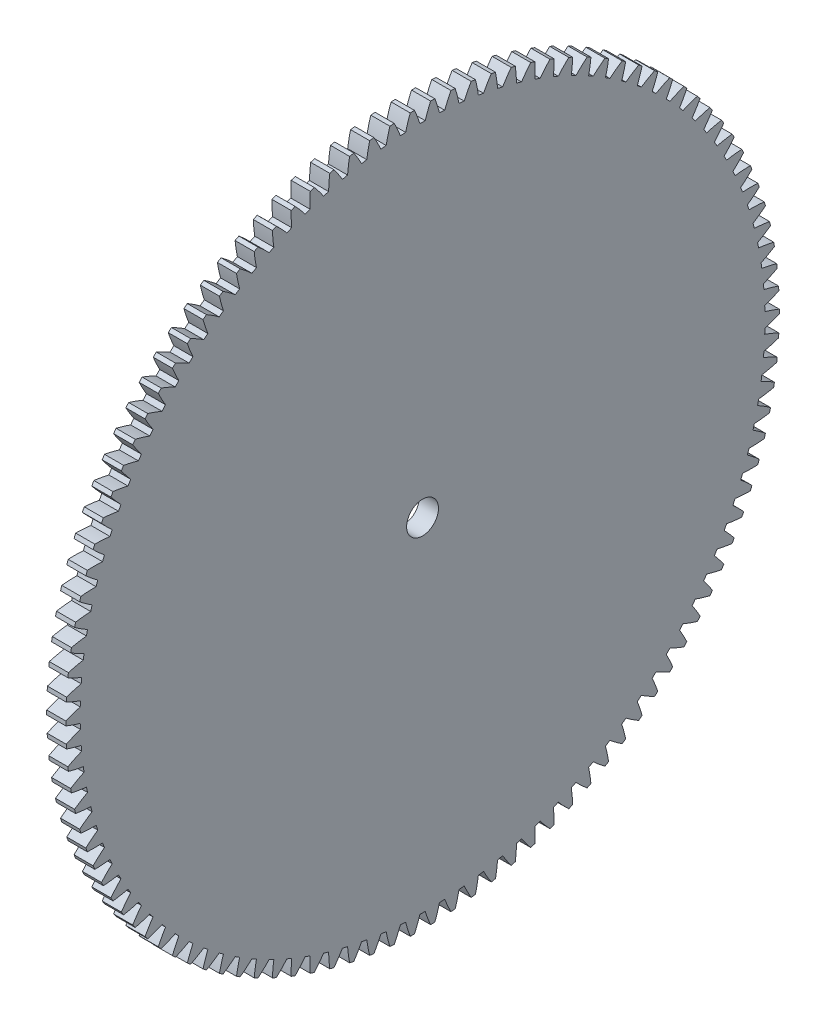
SolidWorks part; units mm, degrees
ref_plane "Plane1" through (0, 0, 0) normal (0, 0, 1) x (1, 0, 0)
ref_plane "Plane2" through (0, 0, 0) normal (0, 1, 0) x (1, 0, 0)
ref_plane "Plane3" through (0, 0, 0) normal (1, 0, 0) x (0, 0, -1)
sketch "HoldingSke" plane through (0, 0, 0) normal (0, 1, 0) x (1, 0, 0)
  line L0 (0, 0) -> (-0.342, -0.9397)
  line L1 (-15, 0) -> (100, 0) construction
  line L2 (0, 0) -> (-2.1039, 2.3779)
  line L3 (0, 0) -> (-11.863, 4.5341)
  line L4 (0, 0) -> (-2.9537, 8.1152)
  line L5 (0, 0) -> (-46.8476, -17.4728)
  line L6 (0, 0) -> (-2.4869, -1.6779)
  line L7 (-2.1039, 2.3779) -> (8.6586, 51.2059)
  line L8 (-76.2, 54.61) -> (-75.3, 54.61)
  line L9 (-71.009, 38.7566) -> (-53.1078, 45.2721)
  line L10 (-76.2, 71.12) -> (104.1128, 71.12)
  line L11 (0, 0) -> (-3, 0)
  line L12 (-76.2, 101.6) -> (-76.162, 101.6)
  line L13 (24.9733, 27.94) -> (52.9518, 28.4284)
  line L14 (24.9733, 27.94) -> (24.9743, 27.94)
  line L15 (24.9733, 27.94) -> (100.4006, 29.5858)
  line L16 (-63.627, -1) -> (-12.827, -1)
  circle A0 centre (0, 0) radius 2.5
  circle A1 centre (0, 0) radius 37.5
  circle A2 centre (0, 0) radius 37.5
  circle A3 centre (0, 0) radius 2.5
  dimension "MHD" = 75
  dimension "Hub_dia" = 75
  dimension "Bore" = 5
  dimension "MBD" = 5
  dimension "Num_teeth" = 110
  dimension "Pitch_radius" = 180.3128
  dimension "Pitch" = 1
  dimension "Width" = 3
  dimension "Overall_len" = 50
  dimension "Show_teeth" = 110
  dimension "Thickness" = 3
  dimension "OAL" = 50.0001
  dimension "T_dim" = 0.9
  dimension "Ap" = 20
  dimension "H" = 19.05
  dimension "Backlash" = 0.038
  dimension "Addendum_fac" = 1
  dimension "Dedendum_fac" = 1.25
  dimension "Clearance_fac" = 0.25
  dimension "Dedendum_add" = 0.001
  dimension "Module" = 1
sketch "BasProSke" plane through (0, 0, 0) normal (0, 1, 0) x (1, 0, 0)
  line L0 (-10, 0) -> (60, 0) construction
  line L1 (0, 0) -> (0, 56)
  line L2 (0, 0) -> (3, 0)
  line L3 (3, 0) -> (3, 56)
  line L4 (3, 56) -> (0, 56)
  dimension "Diameter" = 112
  dimension "Thickness" = 3
revolve "Base-Revolve" add sketch "BasProSke" angle 360 about L0
sketch "TooCutSke" plane through (0, 0, 0) normal (1, 0, 0) x (0, 0, -1)
  line L1 (0, 0) -> (0, 107) construction
  line L2 (0, 0) -> (-0.8519, 54.9934) construction
  line L3 (0, 0) -> (-3.1409, 109.9457) construction
  line L4 (-0.8519, 54.9934) -> (-1.5704, 54.9729) construction
  arc A0 (0.4125, 53.7474) -> (-0.4125, 53.7474) centre (0, 0) ccw
  arc A1 (1.275, 56.0109) -> (-1.275, 56.0109) centre (0, 0) ccw
  circle A2 centre (0, 0) radius 55 construction
  circle A3 centre (0, 0) radius 51.6831 construction
  arc A4 (-0.4125, 53.7474) -> (-1.275, 56.0109) centre (-21.3708, 47.0578) ccw
  arc A5 (1.275, 56.0109) -> (0.4125, 53.7474) centre (21.3708, 47.0578) ccw
  dimension "Root_dia" = 107.498
  dimension "Overcut_dia" = 112.0508
  dimension "Pitch_dia" = 110
  dimension "Base_dia" = 103.3662
  dimension "Flank_rad" = 22
  dimension "Half_ang" = 1.636
  dimension "Half_CT" = 0.7189
extrude "ToothCut" cut sketch "TooCutSke" along normal through all
fillet "Breaks" [suppressed] radius 0.02
fillet "RootFillets" [suppressed] radius 0.251
pattern_circular "TeethCuts" count 110 every 3.273 about axis through (-10, 0, 0) along (1, 0, 0) of "ToothCut", "RootFillets", "Breaks"
sketch "HubNeaOneSke" plane through (0, 0, 0) normal (-1, 0, 0) x (0, 0, 1)
  circle A0 centre (0, 0) radius 37.5
  dimension "Diameter" = 75
extrude "HubNearOne" [suppressed] add sketch "HubNeaOneSke" along normal blind 47.0001
sketch "HubNeaBotSke" plane through (0, 0, 0) normal (-1, 0, 0) x (0, 0, 1)
  circle A0 centre (0, 0) radius 37.5
  dimension "Diameter" = 75
extrude "HubNearBoth" [suppressed] add sketch "HubNeaBotSke" along normal blind 23.5
ref_plane "FarPln" through (3, 0, 0) normal (1, 0, 0) x (0, 0, -1)
sketch "HubFarSke" plane through (3, 0, 0) normal (1, 0, 0) x (0, 0, -1)
  circle A0 centre (0, 0) radius 37.5
  dimension "Diameter" = 75
extrude "HubFar" [suppressed] add sketch "HubFarSke" along normal blind 23.5
sketch "BorSke" plane through (0, 0, 0) normal (1, 0, 0) x (0, 0, -1)
  circle A0 centre (0, 0) radius 2.5
  dimension "Diameter" = 5
extrude "Bore" cut sketch "BorSke" along normal mid plane 100.0001
sketch "KeySke" plane through (0, 0, 0) normal (1, 0, 0) x (0, 0, -1)
  line L0 (-1, 0) -> (-1, 3.4)
  line L1 (-1, 3.4) -> (1, 3.4)
  line L2 (1, 3.4) -> (1, 0)
  line L3 (0, 0) -> (0, 34) construction
  line L4 (-1, 0) -> (1, 0)
  dimension "Offset" = 3.4
  dimension "Width" = 2
extrude "Keyway" [suppressed] cut sketch "KeySke" along normal mid plane 100.0001
pattern_circular "Keyway2" [suppressed] count 2 every 90 about axis through (-10, 0, 0) along (1, 0, 0)
equation "' \"Module@HoldingSke\" = 6.35"
equation "' \"Num_teeth@HoldingSke\" = 12"
equation "' \"Ap@HoldingSke\" =  20"
equation "' \"Width@HoldingSke\" = 0.5 * 25.4"
equation "' \"Hub_dia@HoldingSke\"= 1 * 25.4"
equation "' \"Overall_len@HoldingSke\" = 1.0 * 25.4"
equation "' \"Bore@HoldingSke\" = 0.75 * 25.4"
equation "' \"T_dim@HoldingSke\" = 0.1 * 25.4"
equation "' \"Width@KeySke\" = 0.25 * 25.4"
equation "' \"Show_teeth@HoldingSke\" = 13"
equation "' \"Backlash@HoldingSke\" = 0.009 * 25.4"
equation "' \"Addendum_fac@HoldingSke\" = 1.0"
equation "' \"Dedendum_fac@HoldingSke\" = 1.25"
equation "' \"Dedendum_add@HoldingSke\" = 0.00005 * 25.4"
equation "' \"Clearance_fac@HoldingSke\" = 0.25"
equation "\"Pitch@HoldingSke\" = 1 / \"Module@HoldingSke\""
equation "\"Overcut_dia@TooCutSke\" = (\"Num_teeth@HoldingSke\" + 2 * \"Addendum_fac@HoldingSke\") / \"Pitch@HoldingSke\" + 0.002 * 25.4"
equation "\"Pitch_dia@TooCutSke\" = \"Num_teeth@HoldingSke\" / \"Pitch@HoldingSke\""
equation "\"Base_dia@TooCutSke\" = \"Num_teeth@HoldingSke\" / \"Pitch@HoldingSke\" * cos((\"Ap@HoldingSke\"  * 3.14159265 / 180))"
equation "\"Root_dia@TooCutSke\" = (\"Num_teeth@HoldingSke\" + 2) / \"Pitch@HoldingSke\" - 2 * (\"Addendum_fac@HoldingSke\" + \"Dedendum_fac@HoldingSke\") / \"Pitch@HoldingSke\" - \"Dedendum_add@HoldingSke\" * 2"
equation "\"Half_ang@TooCutSke\" = 180 / \"Num_teeth@HoldingSke\""
equation "\"Half_CT@TooCutSke\" = \"Num_teeth@HoldingSke\" / \"Pitch@HoldingSke\" * sin((3.14159265 / 2 / \"Num_teeth@HoldingSke\")) / 2 - 7 * \"Backlash@HoldingSke\" / 4"
equation "\"Flank_rad@TooCutSke\" = \"Num_teeth@HoldingSke\" / \"Pitch@HoldingSke\" / 5"
equation "\"Radius@RootFillets\" = \"Clearance_fac@HoldingSke\" / \"Pitch@HoldingSke\" + \"Dedendum_add@HoldingSke\""
equation "\"Break_rad@Breaks\" = 0.02 / \"Pitch@HoldingSke\""
equation "\"Thickness@HoldingSke\" = \"Width@HoldingSke\""
equation "\"OAL@HoldingSke\" = \"Thickness@HoldingSke\""
equation "\"MHD@HoldingSke\" = (\"Num_teeth@HoldingSke\" + 2) / \"Pitch@HoldingSke\" - 2 * (\"Addendum_fac@HoldingSke\" + \"Dedendum_fac@HoldingSke\")  / \"Pitch@HoldingSke\" - \"Dedendum_add@HoldingSke\" * 2"
equation "\"MBD@HoldingSke\" = (\"Num_teeth@HoldingSke\" + 2) / \"Pitch@HoldingSke\" - 2 * (\"Addendum_fac@HoldingSke\" + \"Dedendum_fac@HoldingSke\")  / \"Pitch@HoldingSke\" - \"Dedendum_add@HoldingSke\" * 2 - 0.002 * 25.4"
equation "\"MHD@HoldingSke\" = ((sgn( \"MHD@HoldingSke\" - \"Hub_dia@HoldingSke\" )-1)*( \"MHD@HoldingSke\" - \"Hub_dia@HoldingSke\" ))/-2+ \"Hub_dia@HoldingSke\""
equation "\"MBD@HoldingSke\" = ((sgn( \"MBD@HoldingSke\" - \"Bore@HoldingSke\" )-1)*( \"MBD@HoldingSke\" - \"Bore@HoldingSke\" ))/-2+ \"Bore@HoldingSke\""
equation "\"OAL@HoldingSke\" = ((sgn( \"OAL@HoldingSke\" - \"Overall_len@HoldingSke\" )+1)*( \"OAL@HoldingSke\" - \"Overall_len@HoldingSke\" ))/2 + \"Overall_len@HoldingSke\" + 0.000002 * 25.4"
equation "\"Num_teeth@TeethCuts\" = int( \"Show_teeth@HoldingSke\" ) + 1"
equation "\"Num_teeth@TeethCuts\" = ((sgn( \"Num_teeth@TeethCuts\" - \"Num_teeth@HoldingSke\" )-1)*( \"Num_teeth@TeethCuts\" - \"Num_teeth@HoldingSke\" ))/-2+ \"Num_teeth@HoldingSke\""
equation "\"Num_teeth@TeethCuts\" = ((sgn( \"Num_teeth@TeethCuts\" - 2.0)+1)*( \"Num_teeth@TeethCuts\" - 2.0))/2 +2.0"
equation "\"Angle@TeethCuts\" = 360.0 / \"Num_teeth@HoldingSke\""
equation "\"Diameter@BasProSke\" = (\"Num_teeth@HoldingSke\" + 2 * \"Addendum_fac@HoldingSke\") / \"Pitch@HoldingSke\""
equation "\"Thickness@BasProSke\"  = \"Thickness@HoldingSke\""
equation "' \"Fillet_rad@BasProSke\" =  \"Thickness@HoldingSke\" * 0.05"
equation "\"MHD@HoldingSke\" = ((sgn( \"MHD@HoldingSke\" - \"Root_dia@TooCutSke\" )-1)*( \"MHD@HoldingSke\" - \"Root_dia@TooCutSke\" ))/-2+ \"Root_dia@TooCutSke\""
equation "\"Diameter@HubNeaOneSke\" = \"MHD@HoldingSke\""
equation "\"Length@HubNearOne\" = \"OAL@HoldingSke\" - \"Thickness@BasProSke\""
equation "\"Diameter@HubNeaBotSke\" = \"MHD@HoldingSke\""
equation "\"Length@HubNearBoth\" = ( \"OAL@HoldingSke\" - \"Thickness@BasProSke\" ) / 2.0"
equation "\"Thickness@FarPln\" = \"Thickness@BasProSke\""
equation "\"Diameter@HubFarSke\" = \"MHD@HoldingSke\""
equation "\"Length@HubFar\" = ( \"OAL@HoldingSke\" - \"Thickness@BasProSke\" ) / 2.0"
equation "\"Diameter@BorSke\" = \"MBD@HoldingSke\""
equation "\"D1@Bore\" = \"OAL@HoldingSke\" * 2.0"
equation "\"D1@Keyway\" = \"OAL@HoldingSke\" * 2.0"
equation "\"Offset@KeySke\" = \"T_dim@HoldingSke\" + \"MBD@HoldingSke\" / 2.0"
